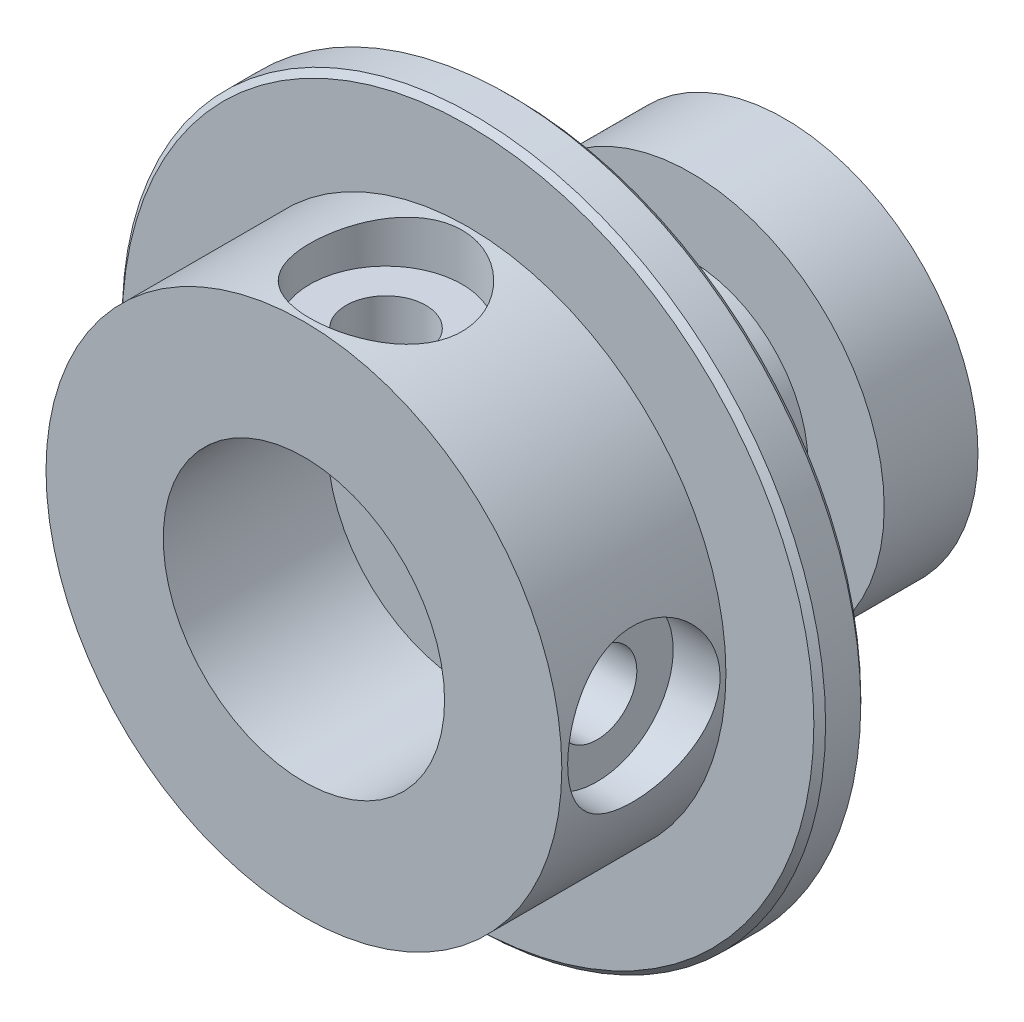
SolidWorks part; units mm, degrees
material "AISI 1020"
ref_plane "Front Plane" through (0, 0, 0) normal (0, 0, 1) x (1, 0, 0)
ref_plane "Top Plane" through (0, 0, 0) normal (0, 1, 0) x (1, 0, 0)
ref_plane "Right Plane" through (0, 0, 0) normal (1, 0, 0) x (0, 0, -1)
sketch "Sketch1" plane through (0, 0, 0) normal (0, 1, 0) x (1, 0, 0)
  line L0 (0, -17.8725) -> (0, 33.6003) construction
  line L1 (6, 0) -> (0, 0)
  line L2 (15, 0) -> (11, 0)
  line L3 (15, 0) -> (15, 2)
  line L4 (15, 2) -> (8.25, 2)
  line L5 (0, 0) -> (0, 6.5)
  line L7 (6, 0) -> (6, -7)
  line L8 (0, 6.5) -> (8.25, 6.5)
  line L9 (8.25, 2) -> (8.25, 6.5)
  line L10 (6, -7) -> (11, -7)
  line L11 (11, 0) -> (11, -7)
  dimension "D1" = 15
  dimension "D2" = 2
  dimension "D3" = 8.25
  dimension "D4" = 4.5
  dimension "D5" = 6
  dimension "D7" = 7
  dimension "D8" = 5
revolve "Revolve1" add sketch "Sketch1" angle 360 about L0
chamfer "Chamfer1" distance 0.25 angle 45 2 edges at (15, 0, 0) (15, 0, -2)
sketch "Sketch2" plane through (0, 0, -6.5) normal (0, 0, -1) x (-1, 0, 0)
  circle A0 centre (0, 0) radius 2.5
  dimension "D1" = 5
extrude "Cut-Extrude1" cut sketch "Sketch2" against normal blind 10
hole_wizard "CBORE for M3 Cheese Head Screw1" positions "3DSketch1" profile "Sketch4" counterbore size "M3" standard "ISO"
sketch3d "3DSketch1"
  point P0 (0, 11, 3.5)
  point P2 (11, 0, 3.5)
  dimension "D1" = 3.5
  dimension "D2" = 3.5
sketch "Sketch4" plane through (0, 11, 3.5) normal (1, 0, 0) x (0, 0, 1)
  line L0 (0, 0) -> (0, 11.0215)
  line L1 (0, 11.0215) -> (1.7, 10)
  line L2 (1.7, 10) -> (1.7, 2)
  line L3 (1.7, 2) -> (3.25, 2)
  line L4 (3.25, 2) -> (3.25, 0)
  line L5 (3.25, 0) -> (0, 0)
  line L10 (0, 11.0215) -> (-1.7, 10) construction
  line L11 (0, -6.35) -> (0, 107.95) construction
  dimension "Hole Dia." = 3.4
  dimension "Hole Depth" = 10
  dimension "C'Bore Dia." = 6.5
  dimension "C'Bore Depth" = 2
  dimension "Drill Angle" = 118
sketch "Sketch5" plane through (0, 0, 0) normal (0, 1, 0) x (1, 0, 0)
  line L0 (2.5, 3.2376) -> (2.5, 13.5)
  line L1 (5, 9.5) -> (5, 3.2376)
  line L2 (5, 3.2376) -> (2.5, 3.2376)
  line L3 (2.5, 13.5) -> (8.25, 13.5)
  line L4 (0, 0) -> (0, 19.4667) construction
  line L5 (8.25, 13.5) -> (8.25, 9.5)
  line L6 (8.25, 9.5) -> (5, 9.5)
  line L7 (8.25, 6.5) -> (-8.25, 6.5) construction
  dimension "D1" = 5
  dimension "D2" = 10
  dimension "D3" = 16.5
  dimension "D4" = 3
  dimension "D5" = 4
revolve "Revolve2" add sketch "Sketch5" angle 360 about L4
